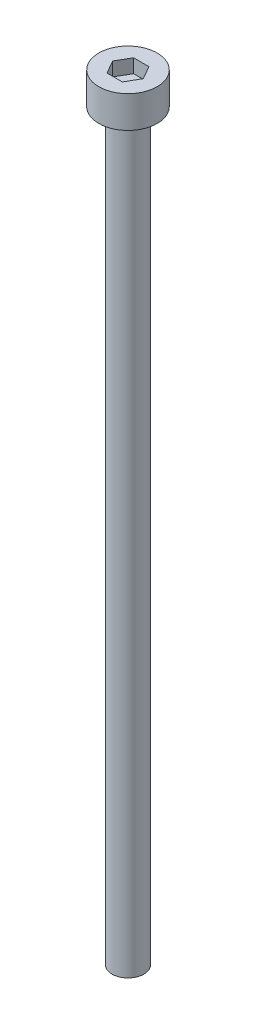
SolidWorks part; units mm, degrees
material "AISI 304"
ref_plane "前视基准面" through (0, 0, 0) normal (0, 0, 1) x (1, 0, 0)
ref_plane "上视基准面" through (0, 0, 0) normal (0, 1, 0) x (1, 0, 0)
ref_plane "右视基准面" through (0, 0, 0) normal (1, 0, 0) x (0, 0, -1)
sketch "草图1" plane through (0, 0, 0) normal (0, 1, 0) x (1, 0, 0)
  circle A0 centre (0, 0) radius 2.75
  dimension "D1" = 5.5
extrude "杯头" add sketch "草图1" along normal blind 3
sketch "草图2" plane through (0, 3, 0) normal (0, 1, 0) x (1, 0, 0)
  line L1 (1.4434, 0) -> (0.7217, 1.25)
  line L2 (0.7217, 1.25) -> (-0.7217, 1.25)
  line L3 (-0.7217, 1.25) -> (-1.4434, 0)
  line L4 (-1.4434, 0) -> (-0.7217, -1.25)
  line L5 (-0.7217, -1.25) -> (0.7217, -1.25)
  line L6 (0.7217, -1.25) -> (1.4434, 0)
  circle A0 centre (0, 0) radius 1.25 construction
  dimension "D1" = 2.5
extrude "内六角口" cut sketch "草图2" against normal blind 1.3
sketch "草图3" plane through (0, 0, 0) normal (0, -1, 0) x (1, 0, 0)
  circle A0 centre (0, 0) radius 1.5
  dimension "D1" = 3
extrude "螺纹长" add sketch "草图3" along normal blind 70
